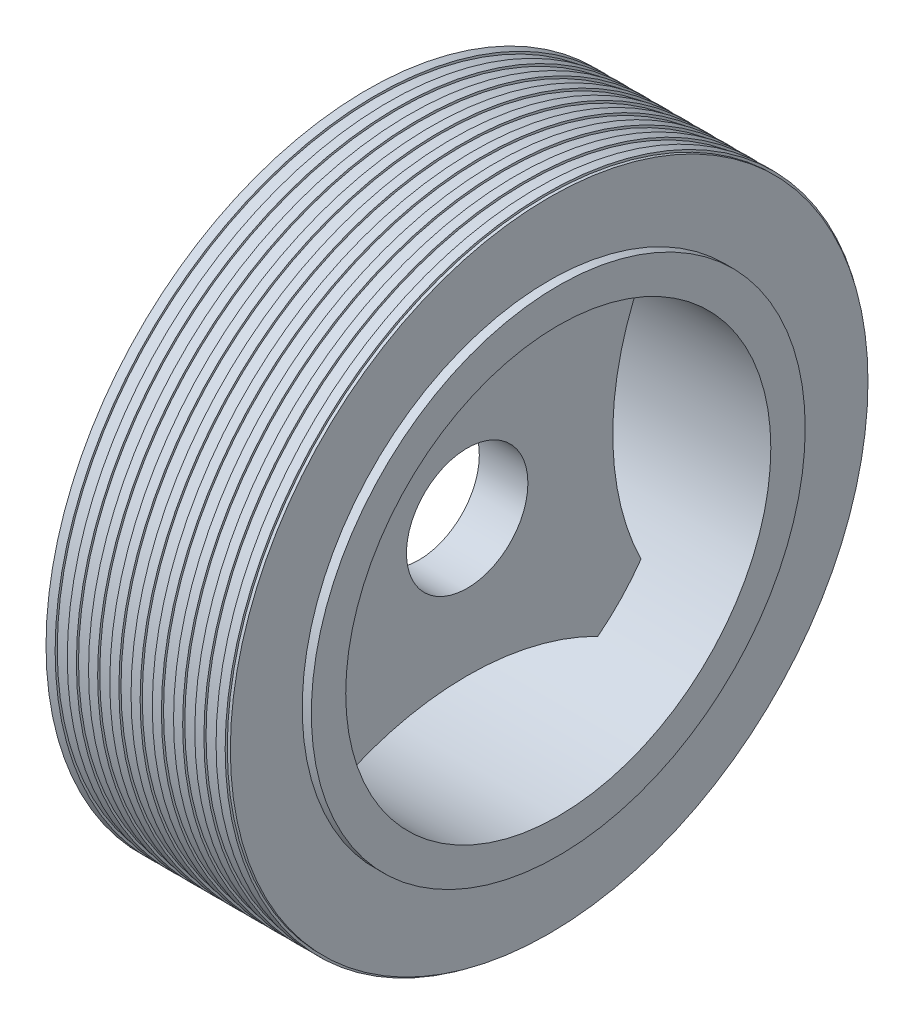
SolidWorks part; units mm, degrees
ref_plane "Front Plane" through (0, 0, 0) normal (0, 0, 1) x (1, 0, 0)
ref_plane "Top Plane" through (0, 0, 0) normal (0, 1, 0) x (1, 0, 0)
ref_plane "Right Plane" through (0, 0, 0) normal (1, 0, 0) x (0, 0, -1)
sketch "Sketch1" plane through (0, 0, 0) normal (0, 0, 1) x (1, 0, 0)
  line L0 (-60.3766, 0) -> (78.6792, 0) construction
  line L1 (25, 75) -> (30, 75)
  line L2 (-30, 105) -> (30, 105)
  line L3 (-30, 105) -> (-30, 75)
  line L4 (-30, 75) -> (-25, 75)
  line L5 (30, 105) -> (30, 75)
  line L7 (-25, 75) -> (-25, 100)
  line L8 (-25, 100) -> (25, 100)
  line L9 (25, 75) -> (25, 100)
  line L10 (-23, 104.7028) -> (-20, 104.7028)
  line L11 (-30, 105.7028) -> (-27, 105.7028)
  line L12 (-30, 105.7028) -> (-30, 104.7028)
  line L13 (-30, 104.7028) -> (-27, 104.7028)
  line L14 (-27, 105.7028) -> (-27, 104.7028)
  line L15 (-23, 105.7028) -> (-23, 104.7028)
  line L16 (-23, 105.7028) -> (-20, 105.7028)
  line L17 (-20, 105.7028) -> (-20, 104.7028)
  line L18 (-16, 104.7028) -> (-13, 104.7028)
  line L19 (-16, 105.7028) -> (-16, 104.7028)
  line L20 (-16, 105.7028) -> (-13, 105.7028)
  line L21 (-13, 105.7028) -> (-13, 104.7028)
  line L22 (-9, 104.7028) -> (-6, 104.7028)
  line L23 (-9, 105.7028) -> (-9, 104.7028)
  line L24 (-9, 105.7028) -> (-6, 105.7028)
  line L25 (-6, 105.7028) -> (-6, 104.7028)
  line L26 (-2, 104.7028) -> (1, 104.7028)
  line L27 (-2, 105.7028) -> (-2, 104.7028)
  line L28 (-2, 105.7028) -> (1, 105.7028)
  line L29 (1, 105.7028) -> (1, 104.7028)
  line L30 (5, 104.7028) -> (8, 104.7028)
  line L31 (5, 105.7028) -> (5, 104.7028)
  line L32 (5, 105.7028) -> (8, 105.7028)
  line L33 (8, 105.7028) -> (8, 104.7028)
  line L34 (12, 104.7028) -> (15, 104.7028)
  line L35 (12, 105.7028) -> (12, 104.7028)
  line L36 (12, 105.7028) -> (15, 105.7028)
  line L37 (15, 105.7028) -> (15, 104.7028)
  line L38 (19, 104.7028) -> (22, 104.7028)
  line L39 (19, 105.7028) -> (19, 104.7028)
  line L40 (19, 105.7028) -> (22, 105.7028)
  line L41 (22, 105.7028) -> (22, 104.7028)
  line L42 (26, 104.7028) -> (29, 104.7028)
  line L43 (26, 105.7028) -> (26, 104.7028)
  line L44 (26, 105.7028) -> (29, 105.7028)
  line L45 (29, 105.7028) -> (29, 104.7028)
  line L62 (33, 104.7028) -> (36, 104.7028) [skipped]
  line L63 (33, 105.7028) -> (33, 104.7028) [skipped]
  line L64 (33, 105.7028) -> (36, 105.7028) [skipped]
  line L65 (36, 105.7028) -> (36, 104.7028) [skipped]
  line L66 (40, 104.7028) -> (43, 104.7028) [skipped]
  line L67 (40, 105.7028) -> (40, 104.7028) [skipped]
  line L68 (40, 105.7028) -> (43, 105.7028) [skipped]
  line L69 (43, 105.7028) -> (43, 104.7028) [skipped]
  line L70 (47, 104.7028) -> (50, 104.7028) [skipped]
  line L71 (47, 105.7028) -> (47, 104.7028) [skipped]
  line L72 (47, 105.7028) -> (50, 105.7028) [skipped]
  line L73 (50, 105.7028) -> (50, 104.7028) [skipped]
  line L74 (54, 104.7028) -> (57, 104.7028) [skipped]
  line L75 (54, 105.7028) -> (54, 104.7028) [skipped]
  line L76 (54, 105.7028) -> (57, 105.7028) [skipped]
  line L77 (57, 105.7028) -> (57, 104.7028) [skipped]
  dimension "D2" = 30
  dimension "D3" = 105
  dimension "D4" = 75
  dimension "D6" = 5
  dimension "D8" = 1
  dimension "D9" = 3
  dimension "D10" = 13
revolve "Revolve1" add sketch "Sketch1" angle 360 about L0
sketch "Sketch2" plane through (30, 0, 0) normal (1, 0, 0) x (0, 0, -1)
  circle A0 centre (0, 0) radius 20
  circle A1 centre (0, 0) radius 81.3279
  dimension "D1" = 40
extrude "Boss-Extrude1" add sketch "Sketch2" along normal blind 3 and the other way blind 63
sketch "Sketch3" plane through (33, 0, 0) normal (1, 0, 0) x (0, 0, -1)
  circle A0 centre (0, 0) radius 70
  dimension "D1" = 140
extrude "Cut-Extrude1" cut sketch "Sketch3" against normal blind 30
sketch "Sketch4" plane through (-33, 0, 0) normal (-1, 0, 0) x (0, 0, 1)
  circle A0 centre (0, 0) radius 70 construction
  circle A1 centre (0, 0) radius 70
extrude "Cut-Extrude2" cut sketch "Sketch4" against normal blind 20
sketch "Sketch5" plane through (3, 0, 0) normal (1, 0, 0) x (0, 0, -1)
  arc A0 (-57.2416, 40.2914) -> (-57.2416, -40.2914) centre (-140, 0) cw
  circle A1 centre (0, 0) radius 70 construction
  circle A2 centre (0, 0) radius 70 construction
  arc A3 (-43.0346, -55.2089) -> (43.0346, -55.2089) centre (0, -140) cw
  arc A4 (57.2416, 40.2914) -> (57.2416, -40.2914) centre (140, 0) ccw
  arc A5 (-43.0346, 55.2089) -> (43.0346, 55.2089) centre (0, 140) ccw
  arc A6 (-57.2416, 40.2914) -> (-57.2416, -40.2914) centre (0, 0) ccw
  arc A7 (43.0346, 55.2089) -> (-43.0346, 55.2089) centre (0, 0) ccw
  arc A8 (57.2416, -40.2914) -> (57.2416, 40.2914) centre (0, 0) ccw
  arc A9 (-43.0346, -55.2089) -> (43.0346, -55.2089) centre (0, 0) ccw
extrude "Cut-Extrude3" cut sketch "Sketch5" against normal blind 30 and the other way blind 20
sketch "Sketch6" plane through (-13, 0, 0) normal (-1, 0, 0) x (0, 0, 1)
  circle A0 centre (-33.4547, 29.112) radius 2.5935
extrude "Boss-Extrude2" add sketch "Sketch6" along normal blind 2 contours A0
